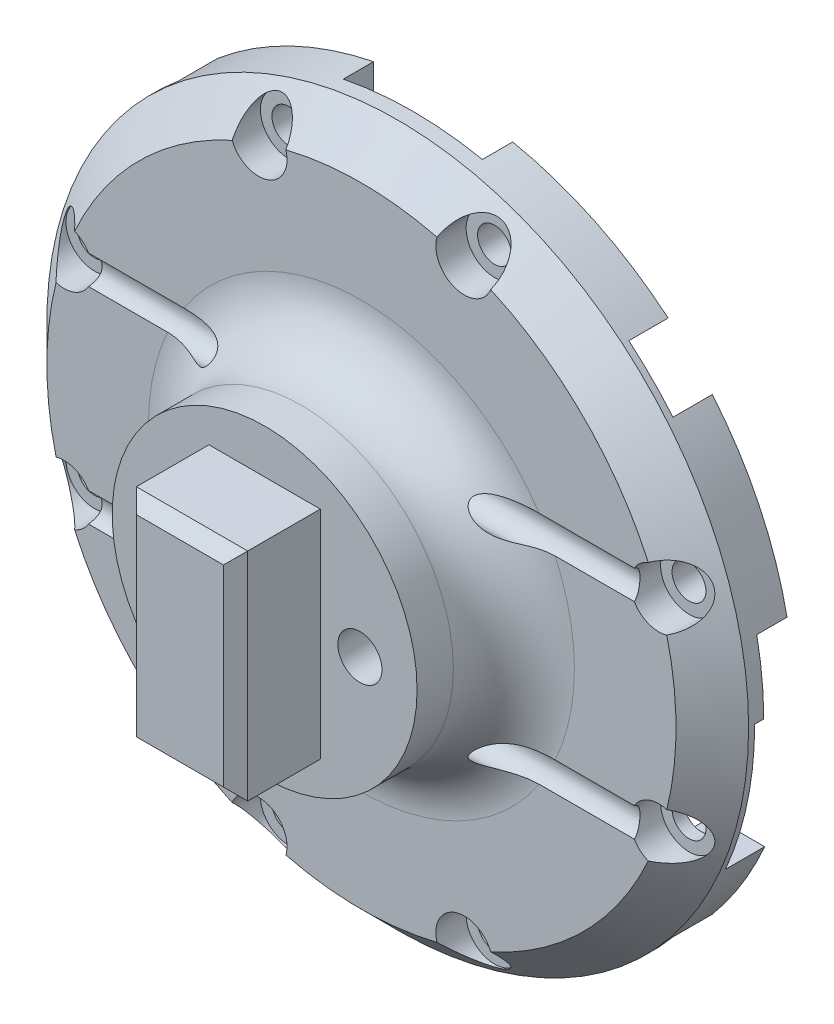
SolidWorks part; units mm, degrees
ref_plane "Front Plane" through (0, 0, 0) normal (0, 0, 1) x (1, 0, 0)
ref_plane "Top Plane" through (0, 0, 0) normal (0, 1, 0) x (1, 0, 0)
ref_plane "Right Plane" through (0, 0, 0) normal (1, 0, 0) x (0, 0, -1)
sketch "Sketch1" plane through (0, 0, 0) normal (0, 0, 1) x (1, 0, 0)
  circle A0 centre (0, 0) radius 29
  dimension "D1" = 58
extrude "Boss-Extrude1" add sketch "Sketch1" along normal blind 6.75
sketch "Sketch3" plane through (0, 0, 0) normal (0, 0, -1) x (-1, 0, 0)
  line L1 (-22.25, -22.25) -> (22.25, -22.25)
  line L2 (-22.25, -22.25) -> (-22.25, 22.25)
  line L3 (-22.25, 22.25) -> (22.25, 22.25)
  line L4 (22.25, -22.25) -> (22.25, 22.25)
  line L5 (-22.25, -22.25) -> (22.25, 22.25) construction
  line L6 (-22.25, 22.25) -> (22.25, -22.25) construction
  point P0 (0, 0)
  dimension "D1" = 44.5
extrude "Cut-Extrude1" cut sketch "Sketch3" against normal blind 3.25
sketch "Sketch4" plane through (0, 0, 6.75) normal (0, 0, 1) x (1, 0, 0)
  circle A0 centre (0, 0) radius 12.6
  dimension "D1" = 25.2
extrude "Boss-Extrude2" add sketch "Sketch4" along normal blind 8
fillet "Fillet1" radius 5 1 edges at (12.6, 0, 6.75)
sketch "Sketch5" plane through (0, 0, 14.75) normal (0, 0, 1) x (1, 0, 0)
  line L0 (0, 8.8489) -> (0, -6.8993) construction
  circle A0 centre (-7.875, 0) radius 1.825
  circle A1 centre (7.875, 0) radius 1.825
  dimension "D1" = 3.65
  dimension "D2" = 15.75
extrude "Cut-Extrude2" cut sketch "Sketch5" against normal through all
sketch "Sketch6" plane through (0, 0, 14.75) normal (0, 0, 1) x (1, 0, 0)
  line L1 (-4.6, 8.95) -> (4.6, 8.95)
  line L2 (-4.6, 8.95) -> (-4.6, -8.95)
  line L3 (-4.6, -8.95) -> (4.6, -8.95)
  line L4 (4.6, 8.95) -> (4.6, -8.95)
  line L5 (-4.6, 8.95) -> (4.6, -8.95) construction
  line L6 (-4.6, -8.95) -> (4.6, 8.95) construction
  point P0 (0, 0)
  dimension "D1" = 9.2
  dimension "D2" = 17.9
extrude "Boss-Extrude3" add sketch "Sketch6" along normal blind 7
chamfer "Chamfer1" distance 1 angle 45 4 edges at (0, -8.95, 21.75) (4.6, 0, 21.75) (0, 8.95, 21.75) (-4.6, 0, 21.75)
sketch "Sketch7" plane through (0, 0, 3.25) normal (0, 0, -1) x (-1, 0, 0)
  circle A0 centre (-7.875, 0) radius 3.25
  circle A1 centre (7.875, 0) radius 3.25
  dimension "D1" = 6.5
extrude "Cut-Extrude3" cut sketch "Sketch7" against normal blind 2.5
fillet "Fillet2" radius 1.5 2 edges at (-11.125, 0, 3.25) (4.625, 0, 3.25)
chamfer "Chamfer2" distance 3 angle 45 1 edges at (29, 0, 6.75)
sketch "Sketch9" plane through (0, 0, 0) normal (1, 0, 0) x (0, 0, -1)
  line L0 (-26.5723, 0) -> (15.7273, 0) construction
  line L2 (-6.75, 17.6) -> (-6.75, -17.6) construction
  circle A0 centre (-7.25, 8.5) radius 1.3
  circle A1 centre (-7.25, -8.5) radius 1.3
  point P7 (-5.3, 7.2531)
  point P8 (-5.8751, 7.2387)
  point P9 (-7.2865, 7.7985)
  point P12 (-6.75, 3.5352)
  dimension "D1" = 2.6
  dimension "D2" = 17
  dimension "D3" = 0.5
extrude "Cut-Extrude5" cut sketch "Sketch9" against normal through all both and the other way through all
sketch "Sketch10" plane through (0, 0, 0) normal (0, 0, -1) x (-1, 0, 0)
  line L0 (5.75, -22.0007) -> (5.75, -34.0342)
  line L1 (22.0007, 5.75) -> (34.0342, 5.75)
  line L2 (22.0007, 5.75) -> (22.0007, -5.75)
  line L3 (22.0007, -5.75) -> (34.0342, -5.75)
  line L4 (34.0342, 5.75) -> (34.0342, -5.75)
  line L5 (5.75, -22.0007) -> (-5.75, -22.0007)
  line L6 (-5.75, -22.0007) -> (-5.75, -34.0342)
  line L7 (5.75, -34.0342) -> (-5.75, -34.0342)
  line L8 (-22.0007, -5.75) -> (-34.0342, -5.75)
  line L9 (-22.0007, -5.75) -> (-22.0007, 5.75)
  line L10 (-22.0007, 5.75) -> (-34.0342, 5.75)
  line L11 (-34.0342, -5.75) -> (-34.0342, 5.75)
  line L12 (-5.75, 22.0007) -> (-5.75, 34.0342)
  line L13 (-5.75, 22.0007) -> (5.75, 22.0007)
  line L14 (5.75, 22.0007) -> (5.75, 34.0342)
  line L15 (-5.75, 34.0342) -> (5.75, 34.0342)
  point P4 (22.0007, 0)
  point P21 (0, 0)
  dimension "D1" = 11.5
  dimension "D2" = 4
extrude "Cut-Extrude6" cut sketch "Sketch10" against normal blind 2.5
sketch "Sketch11" plane through (0, 0, 0) normal (0, 0, -1) x (-1, 0, 0)
  line L0 (-36.6727, 0) -> (0, 0) construction
  circle A0 centre (0, 0) radius 26 construction
  circle A1 centre (-24.5713, 8.5) radius 1.4
  circle A2 centre (-24.5713, -8.5) radius 1.4
  circle A3 centre (-8.5, 24.5713) radius 1.4
  circle A4 centre (8.5, 24.5713) radius 1.4
  circle A5 centre (24.5713, 8.5) radius 1.4
  circle A6 centre (24.5713, -8.5) radius 1.4
  circle A7 centre (8.5, -24.5713) radius 1.4
  circle A8 centre (-8.5, -24.5713) radius 1.4
  point P8 (24.1404, 9.6562)
  point P9 (-24.4531, 8.8344)
  point P10 (24.4819, -8.7541)
  point P23 (0, 0)
  dimension "D1" = 52
  dimension "D3" = 2.8
  dimension "D4" = 17
  dimension "D2" = 4
extrude "Cut-Extrude7" cut sketch "Sketch11" against normal through all
sketch "Sketch12" plane through (0, 0, 6.75) normal (0, 0, 1) x (1, 0, 0)
  circle A0 centre (-24.5713, 8.5) radius 2.35
  circle A1 centre (-24.5713, -8.5) radius 2.35
  circle A2 centre (8.5, 24.5713) radius 2.35
  circle A3 centre (-8.5, 24.5713) radius 2.35
  circle A4 centre (24.5713, -8.5) radius 2.35
  circle A5 centre (24.5713, 8.5) radius 2.35
  circle A6 centre (-8.5, -24.5713) radius 2.35
  circle A7 centre (8.5, -24.5713) radius 2.35
  point P21 (0, 0)
  dimension "D1" = 4.7
  dimension "D2" = 4
extrude "Cut-Extrude8" cut sketch "Sketch12" against normal blind 2.5
sketch "Sketch13" plane through (0, 0, 3.25) normal (0, 0, -1) x (-1, 0, 0)
  line L0 (-22.25, 18.5994) -> (-22.25, -18.5994) construction
  line L1 (-22.15, 14.75) -> (-15.65, 14.75)
  line L2 (-22.15, 14.75) -> (-22.15, 8.25)
  line L3 (-22.15, 8.25) -> (-15.65, 8.25)
  line L4 (-15.65, 14.75) -> (-15.65, 8.25)
  line L5 (18.5994, 22.25) -> (-18.5994, 22.25) construction
  line L6 (14.75, 22.15) -> (14.75, 15.65)
  line L7 (14.75, 22.15) -> (8.25, 22.15)
  line L8 (8.25, 22.15) -> (8.25, 15.65)
  line L9 (14.75, 15.65) -> (8.25, 15.65)
  line L10 (22.15, -14.75) -> (15.65, -14.75)
  line L11 (22.15, -14.75) -> (22.15, -8.25)
  line L12 (22.15, -8.25) -> (15.65, -8.25)
  line L13 (15.65, -14.75) -> (15.65, -8.25)
  line L14 (-14.75, -22.15) -> (-14.75, -15.65)
  line L15 (-14.75, -22.15) -> (-8.25, -22.15)
  line L16 (-8.25, -22.15) -> (-8.25, -15.65)
  line L17 (-14.75, -15.65) -> (-8.25, -15.65)
  point P23 (0, 0)
  dimension "D1" = 0.1
  dimension "D2" = 7.5
  dimension "D4" = 6.5
  dimension "D3" = 4
extrude "Cut-Extrude9" cut sketch "Sketch13" against normal blind 2.25
chamfer "Chamfer5" distance 1 angle 45 12 edges at (-14.75, 18.9, 3.25) (-11.5, 15.65, 3.25) (-8.25, 18.9, 3.25) (14.75, -18.9, 3.25) (11.5, -15.65, 3.25) (8.25, -18.9, 3.25) (-18.9, -8.25, 3.25) (-15.65, -11.5, 3.25) (-18.9, -14.75, 3.25) (18.9, 8.25, 3.25) (15.65, 11.5, 3.25) (18.9, 14.75, 3.25)
sketch "Sketch14" plane through (0, 0, 0) normal (0, 0, -1) x (-1, 0, 0)
  line L1 (-35.1198, 0) -> (-19.2322, 0)
  line L2 (-35.1198, 0) -> (-35.1198, -11.6)
  line L3 (-35.1198, -11.6) -> (-19.2322, -11.6)
  line L4 (-19.2322, 0) -> (-19.2322, -11.6)
  dimension "D1" = 11.6
extrude "Cut-Extrude10" cut sketch "Sketch14" against normal up to surface (3.25 mm away) up to face at (18.4, 11.5, 3.25)
sketch "Sketch15" plane through (0, 0, 6.75) normal (0, 0, 1) x (1, 0, 0)
  line L0 (0, 0) -> (11.6673, 11.6673) construction
  line L1 (0, 0) -> (36.7921, 0) construction
  circle A0 centre (11.6673, 11.6673) radius 12.5
  circle A1 centre (0, 0) radius 29 construction
  dimension "D2" = 25
  dimension "D1" = 45
